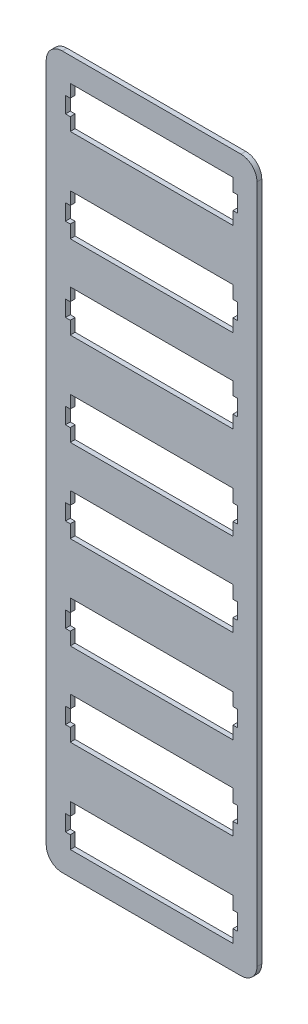
SolidWorks part; units mm, degrees
ref_plane "Ebene vorne" through (0, 0, 0) normal (0, 0, 1) x (1, 0, 0)
ref_plane "Ebene oben" through (0, 0, 0) normal (0, 1, 0) x (1, 0, 0)
ref_plane "Ebene rechts" through (0, 0, 0) normal (1, 0, 0) x (0, 0, -1)
sketch "Skizze1" plane through (0, 0, 0) normal (0, 0, 1) x (1, 0, 0)
  line L0 (0, 0) -> (0, 114)
  line L1 (116.5, 15) -> (15, 15)
  line L2 (0, 114) -> (131.5, 114)
  line L3 (131.5, 0) -> (131.5, 114)
  line L4 (116.5, 15) -> (116.5, 41)
  line L5 (116.5, 73) -> (15, 73)
  line L6 (116.5, 73) -> (116.5, 99)
  line L7 (116.5, 99) -> (15, 99)
  line L8 (15, 73) -> (15, 99)
  line L9 (116.5, 73) -> (15, 99) construction
  line L10 (116.5, 99) -> (15, 73) construction
  line L11 (116.5, 41) -> (15, 41)
  line L12 (15, 15) -> (15, 41)
  line L13 (116.5, 15) -> (15, 41) construction
  line L14 (116.5, 41) -> (15, 15) construction
  line L15 (0, 0) -> (131.5, 0)
  line L16 (131.5, 57) -> (0, 57) construction
  line L17 (65.75, 86) -> (65.75, 28) construction
  point P0 (65.75, 86)
  point P10 (65.75, 28)
  dimension "D1" = 101.5
  dimension "D2" = 26
  dimension "D3" = 101.5
  dimension "D4" = 26
  dimension "D5" = 32
  dimension "D6" = 15
  dimension "D8" = 15
extrude "Aufsatz-Linear austragen1" add sketch "Skizze1" along normal blind 3
sketch "Skizze2" plane through (0, 0, 3) normal (0, 0, 1) x (1, 0, 0)
  line L0 (15, 81) -> (12, 81)
  line L1 (12, 81) -> (12, 91)
  line L2 (12, 91) -> (15, 91)
  line L3 (15, 99) -> (15, 73) construction
  line L4 (12, 86) -> (15, 86) construction
  line L5 (15, 91) -> (15, 81)
  line L6 (65.75, 99) -> (65.75, 73) construction
  line L7 (116.5, 99) -> (15, 99) construction
  line L8 (15, 73) -> (116.5, 73) construction
  line L9 (116.5, 91) -> (116.5, 81)
  line L10 (119.5, 91) -> (116.5, 91)
  line L11 (119.5, 81) -> (119.5, 91)
  line L12 (116.5, 81) -> (119.5, 81)
  line L13 (15, 86) -> (15, 28) construction
  line L14 (15, 41) -> (15, 15) construction
  line L15 (15, 23) -> (12, 23)
  line L16 (12, 23) -> (12, 33)
  line L17 (12, 33) -> (15, 33)
  line L18 (15, 33) -> (15, 23)
  line L19 (116.5, 33) -> (116.5, 23)
  line L20 (119.5, 33) -> (116.5, 33)
  line L21 (119.5, 23) -> (119.5, 33)
  line L22 (116.5, 23) -> (119.5, 23)
  line L23 (131.5, 114) -> (0, 114) construction
  line L24 (12, 28) -> (15, 28) construction
  dimension "D1" = 10
  dimension "D2" = 3
  dimension "D3" = 2
extrude "Schnitt-Linear austragen2" cut sketch "Skizze2" against normal up to next (3 mm away)
pattern_linear "Lineares Muster2" count 4 spacing 110 along (0, -1, 0) of "Schnitt-Linear austragen2", "Aufsatz-Linear austragen1"
fillet "Verrundung1" radius 10 4 edges at (0, 114, 1.5) (131.5, 114, 1.5) (131.5, -330, 1.5) (0, -330, 1.5)
